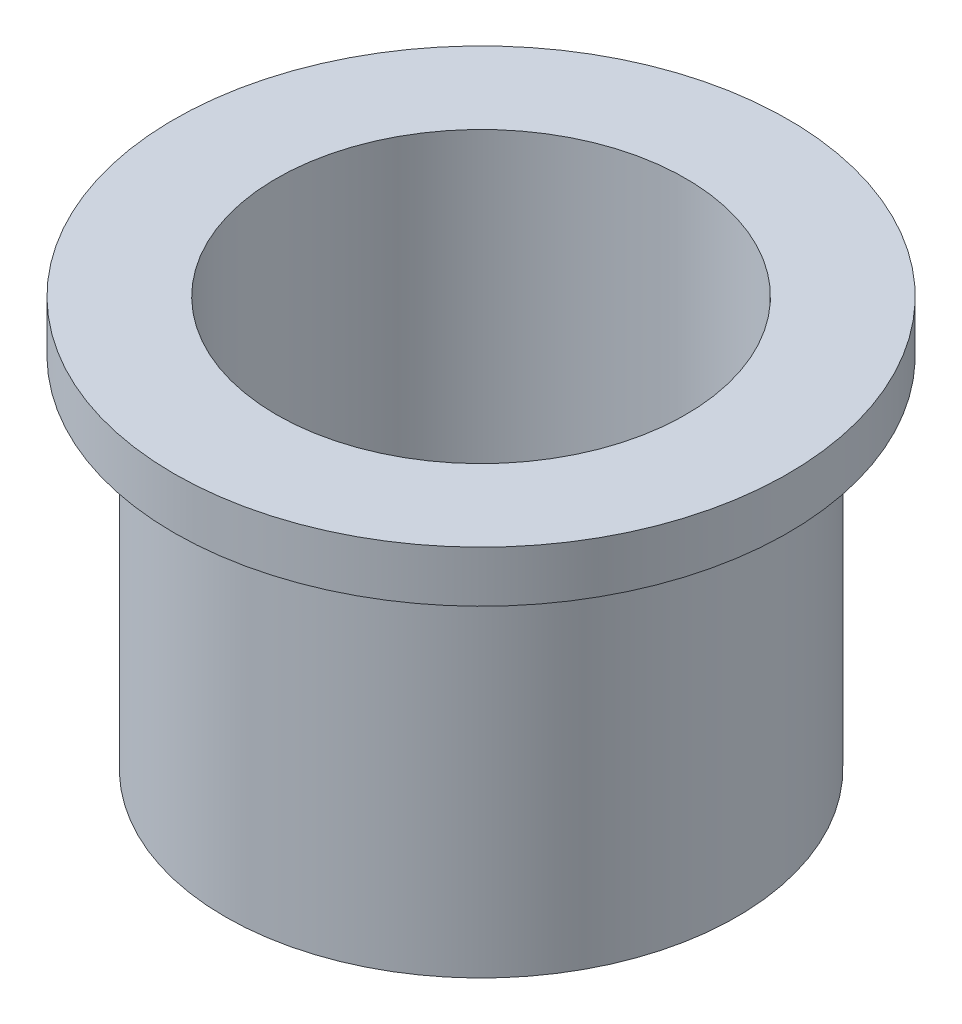
SolidWorks part; units mm, degrees
ref_plane "Front Plane" through (0, 0, 0) normal (0, 0, 1) x (1, 0, 0)
ref_plane "Top Plane" through (0, 0, 0) normal (0, 1, 0) x (1, 0, 0)
ref_plane "Right Plane" through (0, 0, 0) normal (1, 0, 0) x (0, 0, -1)
sketch "Sketch1" plane through (0, 0, 0) normal (0, 1, 0) x (1, 0, 0)
  circle A0 centre (0, 0) radius 6.35
  circle A1 centre (0, 0) radius 7.9375
  dimension "D1" = 12.7
  dimension "D2" = 15.875
extrude "Boss-Extrude1" add sketch "Sketch1" along normal blind 12.7
sketch "Sketch2" plane through (0, 12.7, 0) normal (0, 1, 0) x (1, 0, 0)
  circle A0 centre (0, 0) radius 9.525
  circle A1 centre (0, 0) radius 6.35
  dimension "D1" = 19.05
extrude "Boss-Extrude2" add sketch "Sketch2" against normal blind 1.5875
